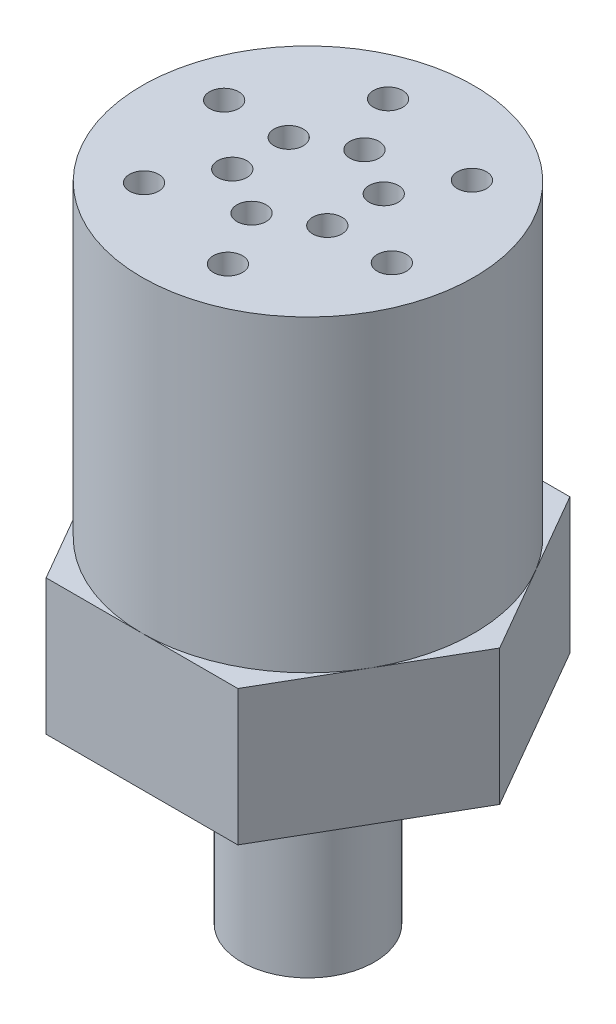
SolidWorks part; units mm, degrees
other "1/2 20 UNF 2A"
ref_plane "Front Plane" through (0, 0, 0) normal (0, 0, 1) x (1, 0, 0)
ref_plane "Top Plane" through (0, 0, 0) normal (0, 1, 0) x (1, 0, 0)
ref_plane "Right Plane" through (0, 0, 0) normal (1, 0, 0) x (0, 0, -1)
sketch "Sketch1" plane through (0, 0, 0) normal (0, 1, 0) x (1, 0, 0)
  circle A0 centre (0, 0) radius 15.875
  dimension "D1" = 31.75
extrude "Neoprene Body" add sketch "Sketch1" along normal blind 29.464
sketch "Sketch2" plane through (0, 0, 0) normal (0, -1, 0) x (1, 0, 0)
  line L0 (-9.1654, 15.875) -> (9.1654, 15.875)
  line L1 (9.1654, 15.875) -> (18.3309, 0)
  line L2 (18.3309, 0) -> (9.1654, -15.875)
  line L3 (9.1654, -15.875) -> (-9.1654, -15.875)
  line L4 (-9.1654, -15.875) -> (-18.3309, 0)
  line L5 (-18.3309, 0) -> (-9.1654, 15.875)
  line L6 (-18.3309, 0) -> (18.3309, 0) construction
  circle A0 centre (0, 0) radius 15.875
  point P4 (0, 0)
  dimension "D1" = 31.75
  dimension "D2" = 120
extrude "Aluminum Bronze Body" add sketch "Sketch2" along normal blind 12.954 separate body contours L1 L2 L3 L4 L5 L0
sketch "Sketch3" plane through (0, -12.954, 0) normal (0, -1, 0) x (-1, 0, 0)
  circle A0 centre (0, 0) radius 6.35
  dimension "D1" = 12.7
extrude "1/2-20 UNF 2A" add sketch "Sketch3" along normal blind 19.05
cosmetic thread "Cosmetic Thread1" parameters "D2"=11.1887
sketch "Sketch4" plane through (0, 29.464, 0) normal (0, 1, 0) x (1, 0, 0)
  line L0 (0, 0) -> (10.745, 0) construction
  line L1 (0, 0) -> (5.3725, -9.3054) construction
  line L2 (0, 0) -> (-5.3725, -9.3054) construction
  line L3 (0, 0) -> (-10.745, 0) construction
  line L4 (0, 0) -> (-5.3725, 9.3054) construction
  line L5 (0, 0) -> (5.3725, 9.3054) construction
  circle A0 centre (10.745, -2.7254) radius 1.397
  circle A1 centre (4.5715, -2.7254) radius 1.397
  circle A2 centre (3.0122, -10.6682) radius 1.397
  circle A3 centre (-0.0745, -5.3218) radius 1.397
  circle A4 centre (-7.7328, -7.9427) radius 1.397
  circle A5 centre (-4.6461, -2.5963) radius 1.397
  circle A6 centre (-10.745, 2.7254) radius 1.397
  circle A7 centre (-4.5715, 2.7254) radius 1.397
  circle A8 centre (-3.0122, 10.6682) radius 1.397
  circle A9 centre (0.0745, 5.3218) radius 1.397
  circle A10 centre (7.7328, 7.9427) radius 1.397
  circle A11 centre (4.6461, 2.5963) radius 1.397
  point P35 (0, 0)
  dimension "D1" = 2.794
  dimension "D2" = 2.794
  dimension "D3" = 6
extrude "Cut-Extrude1" cut sketch "Sketch4" against normal blind 10.16
